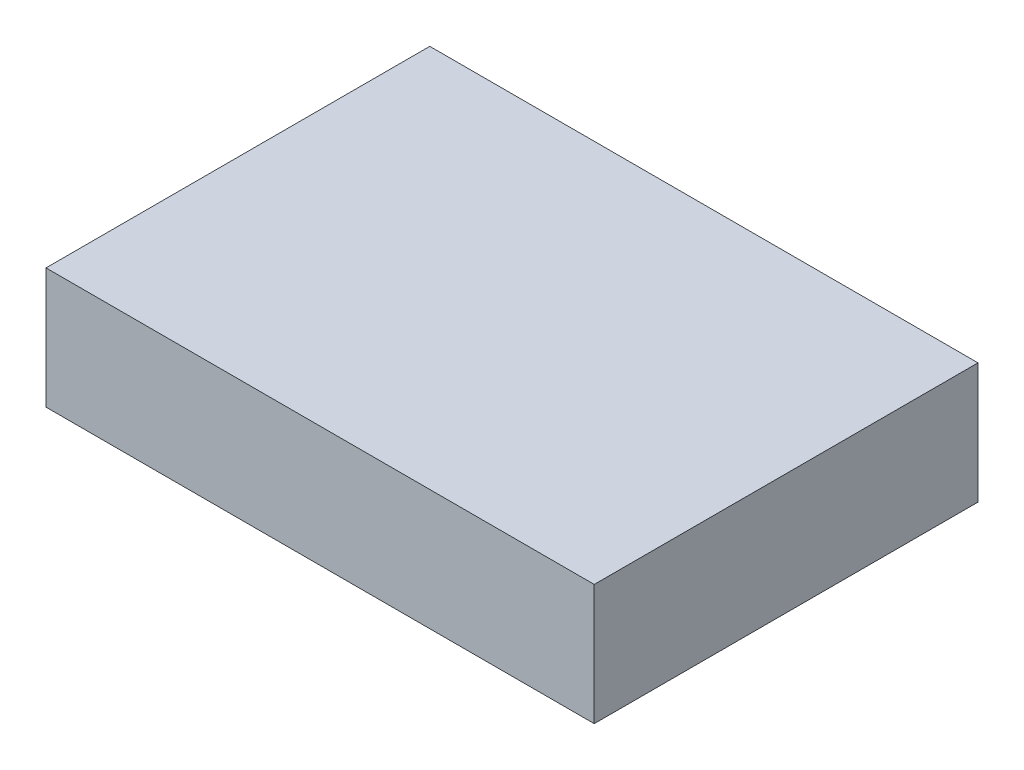
SolidWorks part; units mm, degrees
ref_plane "Front Plane" through (0, 0, 0) normal (0, 0, 1) x (1, 0, 0)
ref_plane "Top Plane" through (0, 0, 0) normal (0, 1, 0) x (1, 0, 0)
ref_plane "Right Plane" through (0, 0, 0) normal (1, 0, 0) x (0, 0, -1)
sketch "Sketch1" plane through (0, 0, 0) normal (0, 1, 0) x (1, 0, 0)
  line L1 (-34.2523, 17.0051) -> (15.7477, 17.0051)
  line L2 (-34.2523, 17.0051) -> (-34.2523, -17.9949)
  line L3 (-34.2523, -17.9949) -> (15.7477, -17.9949)
  line L4 (15.7477, 17.0051) -> (15.7477, -17.9949)
extrude "Boss-Extrude1" add sketch "Sketch1" along normal blind 11
